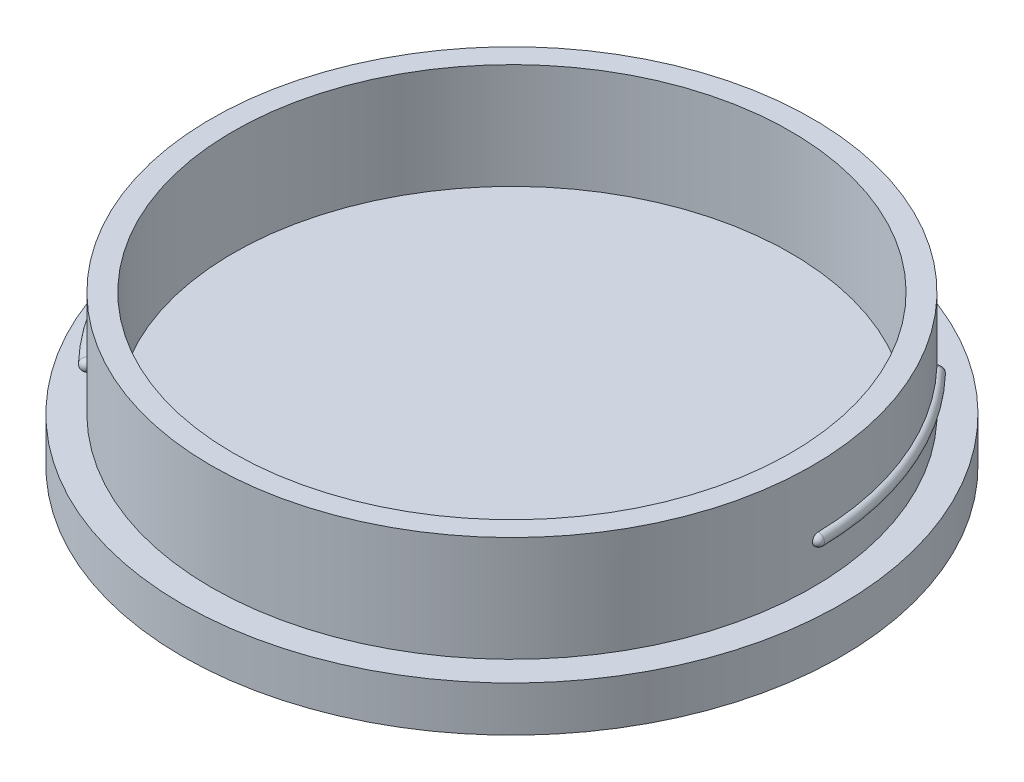
SolidWorks part; units mm, degrees
ref_plane "Płaszczyzna przednia" through (0, 0, 0) normal (0, 0, 1) x (1, 0, 0)
ref_plane "Płaszczyzna górna" through (0, 0, 0) normal (0, 1, 0) x (1, 0, 0)
ref_plane "Płaszczyzna prawa" through (0, 0, 0) normal (1, 0, 0) x (0, 0, -1)
sketch "Szkic1" plane through (0, 0, 0) normal (0, 1, 0) x (1, 0, 0)
  circle A0 centre (0, 0) radius 21.875
  dimension "D1" = 43.75
extrude "Dodanie-wyciągnięcie1" add sketch "Szkic1" along normal blind 3
sketch "Szkic2" plane through (0, 3, 0) normal (0, 1, 0) x (1, 0, 0)
  circle A0 centre (0, 0) radius 19.95
  circle A1 centre (0, 0) radius 18.5
  dimension "D1" = 39.9
  dimension "D2" = 37
extrude "Dodanie-wyciągnięcie2" add sketch "Szkic2" along normal blind 10 from surface at -3 starting at plane "Płaszczyzna górna"
sketch "Szkic3" plane through (0, 3, 0) normal (0, 1, 0) x (1, 0, 0)
  line L0 (0, 0) -> (0, -25.145) construction
  line L2 (-2.25, 22.2616) -> (-2.25, 19.8227)
  line L4 (2.25, 22.2616) -> (2.25, 19.8227)
  circle A0 centre (0, 0) radius 19.95 construction
  arc A1 (2.25, 19.8227) -> (-2.25, 19.8227) centre (0, 0) ccw
  arc A2 (-2.25, 22.2616) -> (2.25, 22.2616) centre (0, 0) cw
  circle A3 centre (0, 0) radius 21.875 construction
  circle A4 centre (0, 0) radius 21.875 construction
  dimension "D3" = 22.375
  dimension "D2" = 21.875
  dimension "D1" = 4.5
extrude "Dodanie-wyciągnięcie3" add sketch "Szkic3" along normal blind 1.4
sketch "Szkic4" plane through (0, 0, 0) normal (0, 0, 1) x (1, 0, 0)
  line L2 (-19.95, 10) -> (-19.95, 3) construction
  line L3 (19.95, 10) -> (-19.95, 10) construction
  line L4 (0, -2.7746) -> (0, 14.1267) construction
  circle A0 centre (-19.95, 5.6) radius 0.4
  dimension "D1" = 0.8
  dimension "D3" = 4.4
revolve "Obrót1" add sketch "Szkic4" angle 45 about L4
fillet "Zaokrąglenie2" radius 0.39 2 edges at (-14.3896, 5.6, 14.3896) (-20.35, 5.6, 0)
pattern_circular "Szyk kołowy5" count 2 over 360 about axis through (0, 10, 0) along (0, -1, 0) of "Zaokrąglenie2", "Obrót1"
equation "\"D3@Szkic3\"=0.5+\"D2@Szkic3\""
equation "\"D3@Szkic4\"=4+\"D1@Szkic4\"/2"
